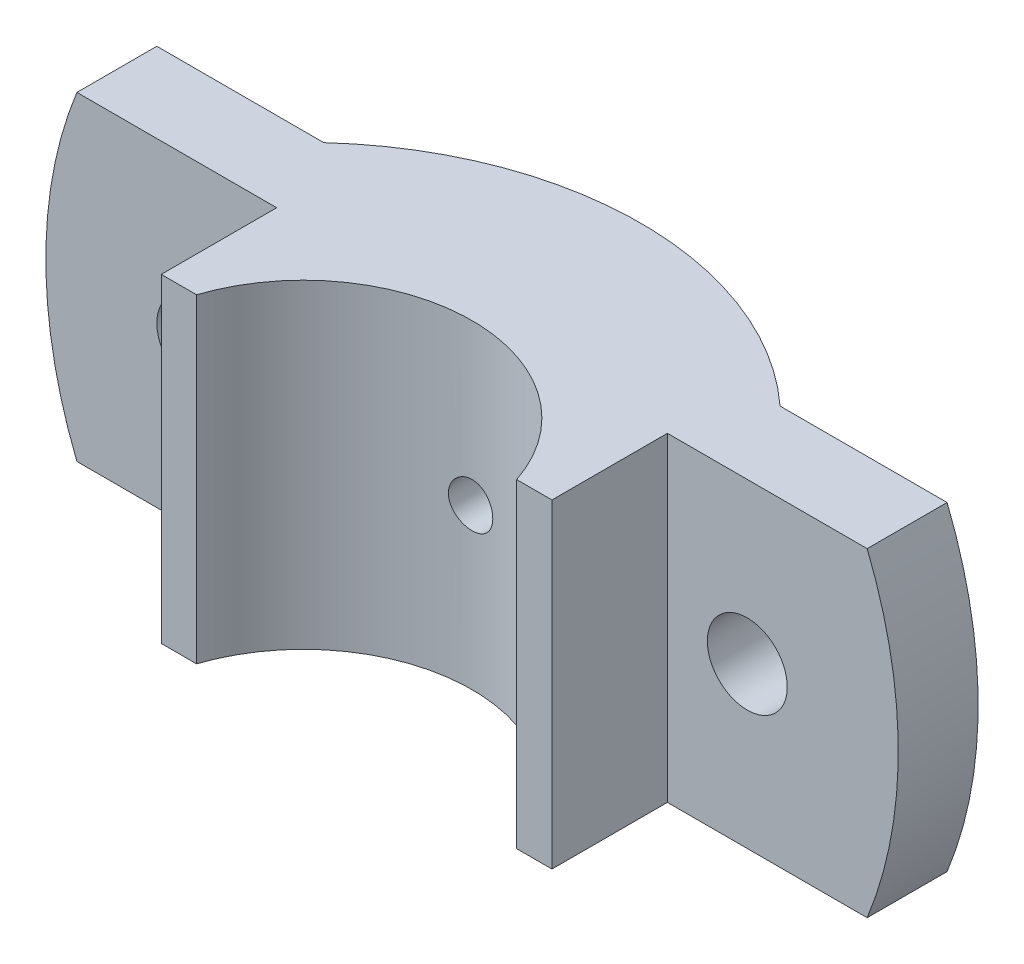
SolidWorks part; units mm, degrees
ref_plane "Front Plane" through (0, 0, 0) normal (0, 0, 1) x (1, 0, 0)
ref_plane "Top Plane" through (0, 0, 0) normal (0, 1, 0) x (1, 0, 0)
ref_plane "Right Plane" through (0, 0, 0) normal (1, 0, 0) x (0, 0, -1)
sketch "Sketch1" plane through (0, 0, 0) normal (0, 1, 0) x (1, 0, 0)
  line L1 (0, 66.3062) -> (0, -74.2828) construction
  line L2 (18.0278, 6) -> (22, 6)
  line L3 (22, 6) -> (22, 19)
  line L4 (22, 19) -> (50, 19)
  line L5 (50, 19) -> (50, 28)
  line L6 (50, 28) -> (25.6905, 28)
  line L7 (-50, 28) -> (-25.6905, 28)
  line L8 (-50, 19) -> (-50, 28)
  line L9 (-22, 19) -> (-50, 19)
  line L10 (-22, 6) -> (-22, 19)
  line L11 (-18.0278, 6) -> (-22, 6)
  arc A0 (25.6905, 28) -> (-25.6905, 28) centre (0, 0) ccw
  arc A1 (18.0278, 6) -> (-18.0278, 6) centre (0, 0) ccw
  dimension "D2" = 19
  dimension "D7" = 38
  dimension "D3" = 6
  dimension "D4" = 13
  dimension "D5" = 19
  dimension "D6" = 19
  dimension "D9" = 100
  dimension "D10" = 9
  dimension "D11" = 44
extrude "Boss-Extrude1" add sketch "Sketch1" along normal mid plane 36
sketch "Sketch2" plane through (0, 0, -28) normal (0, 0, -1) x (-1, 0, 0)
  circle A0 centre (31, 0) radius 4.5
  dimension "D2" = 9
  dimension "D1" = 31
extrude "Cut-Extrude1" cut sketch "Sketch2" against normal through all
sketch "Sketch3" plane through (0, 0, -28) normal (0, 0, -1) x (-1, 0, 0)
  line L0 (25.6905, 18) -> (25.6905, -18) construction
  line L1 (25.6905, 6.6377) -> (25.6905, -6.6377)
  arc A0 (25.6905, 6.6377) -> (25.6905, -6.6377) centre (31, 0) ccw
  dimension "D3" = 8.5
  dimension "D1" = 31
extrude "Cut-Extrude9" cut sketch "Sketch3" along normal through all
sketch "Sketch5" plane through (0, 0, 0) normal (0, 0, 1) x (1, 0, 0)
  line L0 (-50, 18) -> (-50, -18) construction
  line L1 (-25.6905, -18) -> (-50, -18) construction
  line L2 (-25.6905, 18) -> (-50, 18) construction
  line L3 (-50, 18) -> (-50, -18)
  line L4 (-44.4972, -18) -> (-50, -18)
  line L5 (-44.4972, 18) -> (-50, 18)
  arc A0 (-44.4972, 18) -> (-44.4972, -18) centre (0, 0) ccw
  dimension "D1" = 96
extrude "Cut-Extrude10" cut sketch "Sketch5" against normal through all
ref_plane "Plane1" through (0, 0, -38) normal (0, 0, -1) x (-1, 0, 0)
hole_wizard "CBORE for M5 Hex Head Bolt1" positions "3DSketch2" profile "Sketch12" counterbore size "M5" standard "ANSI Metric" end condition through all
sketch3d "3DSketch2"
  point P0 (0, 0, -38)
  dimension "D1" = 0
  dimension "D2" = 0
sketch "Sketch12" plane through (0, 0, -38) normal (1, 0, 0) x (0, 1, 0)
  line L0 (0, 0) -> (0, 32)
  line L1 (0, 32) -> (2.5, 32)
  line L3 (2.5, 32) -> (2.5, 13)
  line L4 (2.5, 13) -> (3, 13)
  line L5 (3, 13) -> (3, 0)
  line L7 (3, 0) -> (0, 0)
  line L11 (0, -6.35) -> (0, 107.95) construction
  dimension "Thru Hole Dia." = 5
  dimension "Thru Hole Depth" = 32
  dimension "C'Bore Dia." = 6
  dimension "C'Bore Depth" = 13
mirror "Mirror1" about plane through (0, 0, 0) normal (1, 0, 0) of "Cut-Extrude1", "Cut-Extrude9", "Cut-Extrude10"
